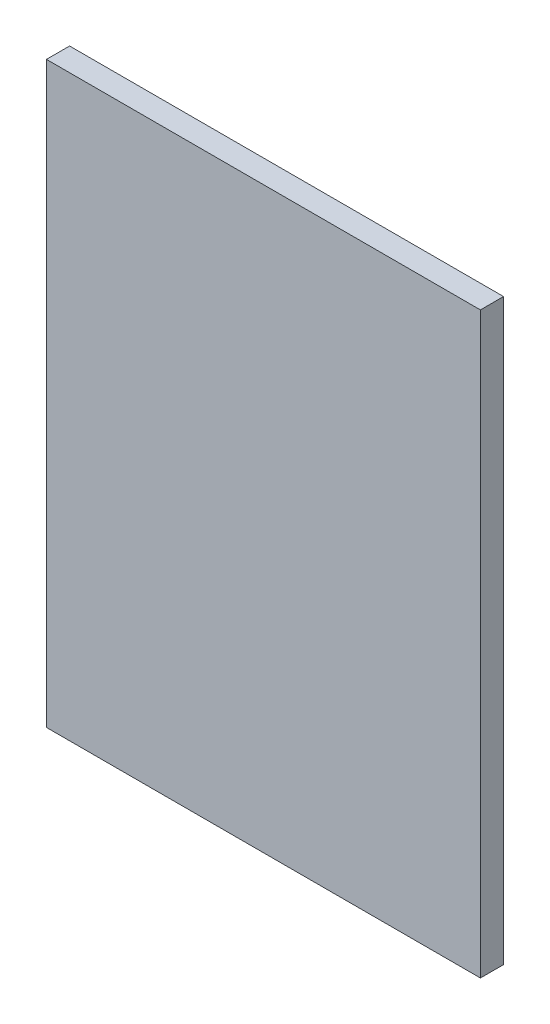
SolidWorks part; units mm, degrees
ref_plane "Front Plane" through (0, 0, 0) normal (0, 0, 1) x (1, 0, 0)
ref_plane "Top Plane" through (0, 0, 0) normal (0, 1, 0) x (1, 0, 0)
ref_plane "Right Plane" through (0, 0, 0) normal (1, 0, 0) x (0, 0, -1)
sketch "Sketch1" plane through (0, 0, 0) normal (0, 0, 1) x (1, 0, 0)
  line L1 (-120.4128, 168.1193) -> (29.5872, 168.1193)
  line L2 (-120.4128, 168.1193) -> (-120.4128, -31.8807)
  line L3 (-120.4128, -31.8807) -> (29.5872, -31.8807)
  line L4 (29.5872, 168.1193) -> (29.5872, -31.8807)
  dimension "D1" = 150
  dimension "D2" = 200
extrude "Boss-Extrude1" add sketch "Sketch1" along normal blind 8
